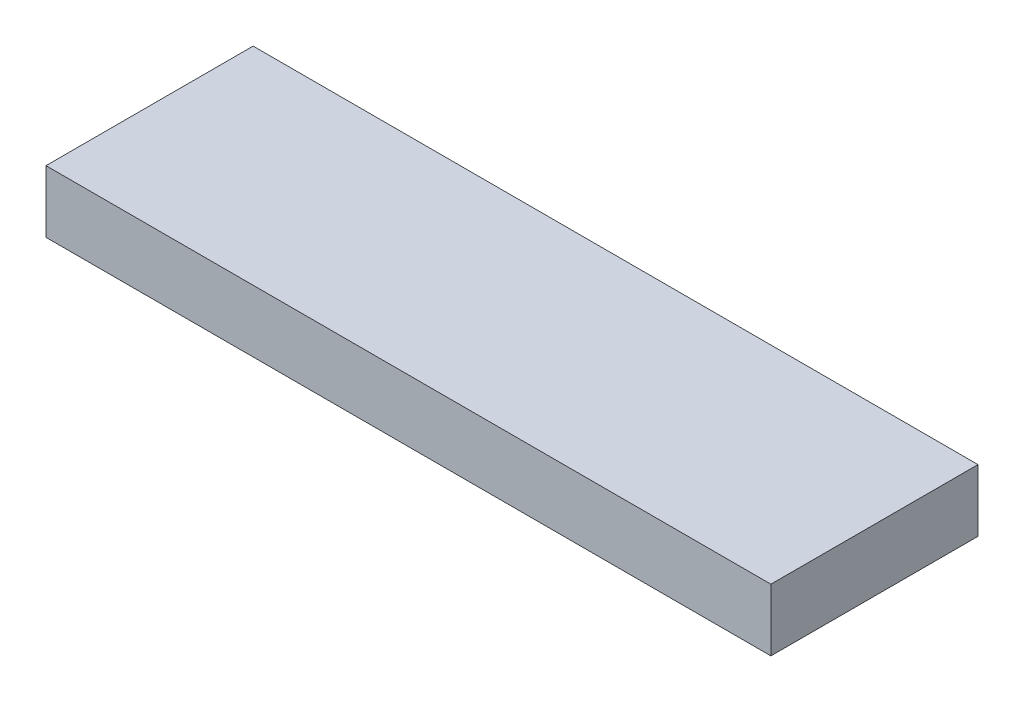
SolidWorks part; units mm, degrees
ref_plane "Спереди" through (0, 0, 0) normal (0, 0, 1) x (1, 0, 0)
ref_plane "Сверху" through (0, 0, 0) normal (0, 1, 0) x (1, 0, 0)
ref_plane "Справа" through (0, 0, 0) normal (1, 0, 0) x (0, 0, -1)
other "Configuration Table"
sketch "Эскиз1" plane through (0, 0, 0) normal (0, 1, 0) x (1, 0, 0)
  line L0 (0, 0) -> (70, 0)
  line L1 (0, 0) -> (0, 20)
  line L2 (0, 20) -> (70, 20)
  line L3 (70, 20) -> (70, 0)
  dimension "D1" = 70
  dimension "D2" = 20
extrude "Скамейка" add sketch "Эскиз1" along normal blind 6
sketch "Эскиз2" plane through (0, 0, 0) normal (0, 1, 0) x (1, 0, 0)
  line L0 (70, 20) -> (0, 20) construction
  line L1 (5.9646, 18) -> (11.9646, 18)
  line L2 (5.9646, 18) -> (5.9646, 2)
  line L3 (5.9646, 2) -> (11.9646, 2)
  line L4 (11.9646, 18) -> (11.9646, 2)
  dimension "D1" = 6
  dimension "D2" = 16
  dimension "D3" = 2
other "Выровнять группу1"
